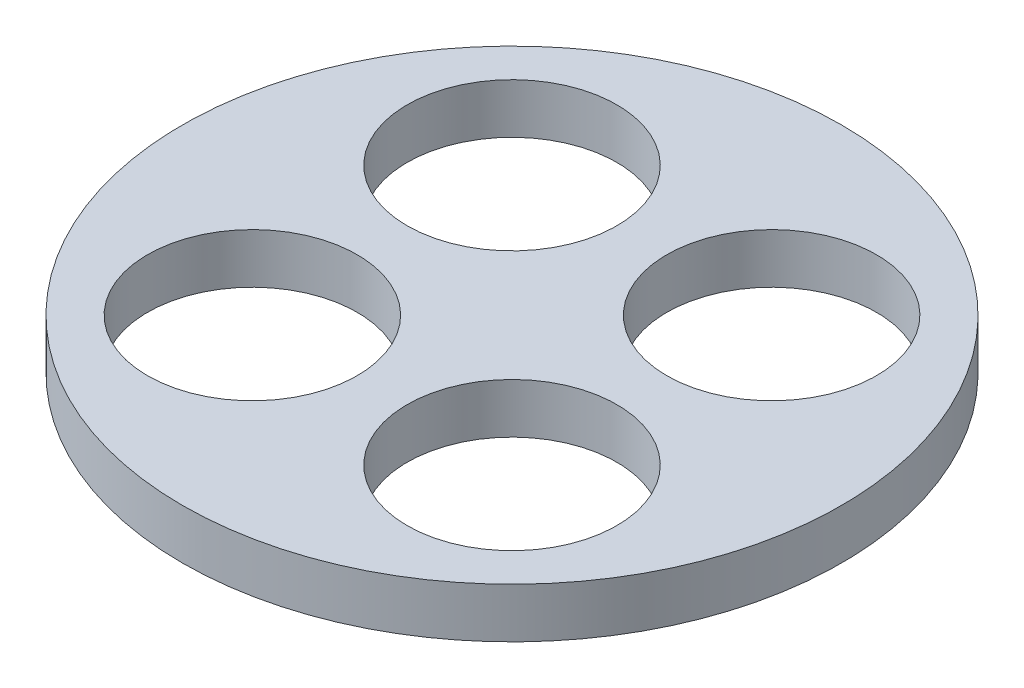
SolidWorks part; units mm, degrees
ref_plane "Front Plane" through (0, 0, 0) normal (0, 0, 1) x (1, 0, 0)
ref_plane "Top Plane" through (0, 0, 0) normal (0, 1, 0) x (1, 0, 0)
ref_plane "Right Plane" through (0, 0, 0) normal (1, 0, 0) x (0, 0, -1)
sketch "Sketch1" plane through (0, 0, 0) normal (0, 1, 0) x (1, 0, 0)
  line L0 (0, -16.5) -> (0, 16.5) construction
  line L1 (-16.5, 0) -> (16.5, 0) construction
  circle A0 centre (0, 0) radius 16.5
  circle A1 centre (6.5, -6.5) radius 5.25
  circle A2 centre (-6.5, -6.5) radius 5.25
  circle A3 centre (-6.5, 6.5) radius 5.25
  circle A4 centre (6.5, 6.5) radius 5.25
  point P18 (0, 0)
  dimension "D1" = 33
  dimension "D2" = 10.5
  dimension "D4" = 6.5
  dimension "D5" = 6.5
  dimension "D3" = 4
extrude "Boss-Extrude1" add sketch "Sketch1" along normal blind 2.5
